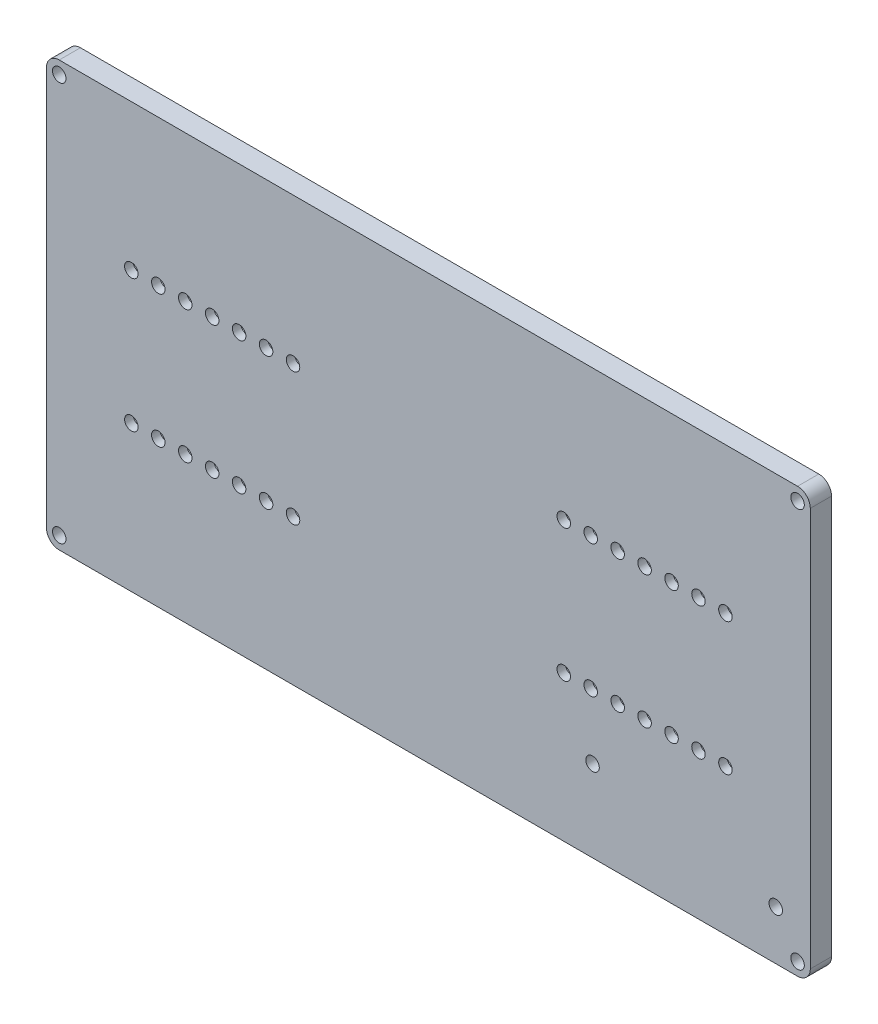
SolidWorks part; units mm, degrees
ref_plane "Front Plane" through (0, 0, 0) normal (0, 0, 1) x (1, 0, 0)
ref_plane "Top Plane" through (0, 0, 0) normal (0, 1, 0) x (1, 0, 0)
ref_plane "Right Plane" through (0, 0, 0) normal (1, 0, 0) x (0, 0, -1)
sketch "Sketch1" plane through (0, 0, 0) normal (0, 0, 1) x (1, 0, 0)
  line L0 (-90, 0) -> (90, 0) construction
  line L1 (-90, 50) -> (90, 50)
  line L2 (-90, 50) -> (-90, -50)
  line L3 (-90, -50) -> (90, -50)
  line L4 (90, 50) -> (90, -50)
  line L5 (-90, 50) -> (90, -50) construction
  line L6 (-90, -50) -> (90, 50) construction
  point P0 (0, 0)
  point P9 (0, 0)
  dimension "D1" = 100
  dimension "D2" = 180
extrude "Boss-Extrude1" add sketch "Sketch1" along normal blind 5 contours L1 L4 L3 L2
sketch "Sketch2" plane through (0, 0, 5) normal (0, 0, 1) x (1, 0, 0)
  line L0 (-90, 0) -> (90, 0) construction
  line L1 (-90, 50) -> (-90, -50) construction
  line L2 (90, 50) -> (90, -50) construction
  line L3 (0, 50) -> (0, -50) construction
  line L4 (-90, 50) -> (90, 50) construction
  line L5 (-90, -50) -> (90, -50) construction
  circle A0 centre (-70, 15.62) radius 1.59
  dimension "D1" = 3.18
  dimension "D2" = 70
  dimension "D3" = 15.62
extrude "Cut-Extrude1" cut sketch "Sketch2" against normal through all
pattern_linear "LPattern1" count 7 spacing 6.35 along (1, 0, 0) count 2 spacing 31.24 along (0, -1, 0) of "Cut-Extrude1"
ref_plane "Plane1" through (0, 0, 0) normal (1, 0, 0) x (0, 0, -1)
mirror "Mirror1" about plane through (0, 0, 0) normal (1, 0, 0) of "LPattern1", "Cut-Extrude1"
ref_plane "Plane2" through (0, 0, 0) normal (0, 1, 0) x (1, 0, 0)
sketch "Sketch4" plane through (0, 0, 0) normal (0, 0, -1) x (-1, 0, 0)
  line L0 (28.9, 15.62) -> (73, 15.62) construction
  line L1 (28.9, 18.22) -> (73, 18.22)
  line L2 (28.9, 18.22) -> (28.9, 13.02)
  line L3 (28.9, 13.02) -> (73, 13.02)
  line L4 (73, 18.22) -> (73, 13.02)
  circle A0 centre (70, 15.62) radius 1.59 construction
  circle A1 centre (70, 15.62) radius 1.59 construction
  circle A2 centre (31.9, 15.62) radius 1.59 construction
  circle A3 centre (31.9, 15.62) radius 1.59 construction
  dimension "D3" = 3
  dimension "D1" = 5.2
  dimension "D2" = 3
extrude "Cut-Extrude3" cut sketch "Sketch4" against normal blind 3
mirror "Mirror4" about plane through (0, 0, 0) normal (0, 1, 0) of "Cut-Extrude3"
mirror "Mirror5" about plane through (0, 0, 0) normal (1, 0, 0) of "Mirror4", "Cut-Extrude3"
fillet "Fillet1" radius 1 16 edges at (-28.9, -18.22, 1.5) (-28.9, -13.02, 1.5) (28.9, -13.02, 1.5) (73, -13.02, 1.5) (73, -18.22, 1.5) (28.9, -18.22, 1.5) (-73, -18.22, 1.5) (-73, -13.02, 1.5) (-73, 13.02, 1.5) (-73, 18.22, 1.5) (-28.9, 18.22, 1.5) (-28.9, 13.02, 1.5) (73, 13.02, 1.5) (73, 18.22, 1.5) (28.9, 13.02, 1.5) (28.9, 18.22, 1.5)
fillet "Fillet2" radius 3 4 edges at (90, -50, 2.5) (-90, -50, 2.5) (-90, 50, 2.5) (90, 50, 2.5)
sketch "Sketch5" plane through (0, 0, 0) normal (0, 0, -1) x (-1, 0, 0)
  line L1 (-81.8636, -38.3983) -> (-38.6836, -38.3983) construction
  line L2 (-81.8636, -38.3983) -> (-81.8636, -30.7783) construction
  line L3 (-81.8636, -30.7783) -> (-38.6836, -30.7783) construction
  line L4 (-38.6836, -38.3983) -> (-38.6836, -30.7783) construction
  circle A2 centre (-81.8636, -38.3983) radius 3
  circle A3 centre (-38.6836, -30.7783) radius 3
  dimension "D5" = 6
  dimension "D6" = 6
  dimension "D1" = 7.62
  dimension "D2" = 43.18
extrude "Boss-Extrude3" add sketch "Sketch5" along normal blind 3
sketch "Sketch11" plane through (0, 0, -3) normal (0, 0, -1) x (-1, 0, 0)
  circle A0 centre (-81.8636, -38.3983) radius 3 construction
  circle A1 centre (-81.8636, -38.3983) radius 3
  circle A2 centre (-81.8636, -38.3983) radius 1.59
  circle A3 centre (-38.6836, -30.7783) radius 1.59
  dimension "D1" = 3.18
  dimension "D2" = 3.18
extrude "Cut-Extrude5" cut sketch "Sketch11" against normal through all both and the other way through all contours A3 | A2
sketch "Sketch12" plane through (0, 0, 0) normal (0, 0, -1) x (-1, 0, 0)
  line L0 (-90, 47) -> (-90, -47) construction
  line L1 (-87, -47) -> (87, -47) construction
  line L2 (-87, -47) -> (-87, 47) construction
  line L3 (-87, 47) -> (87, 47) construction
  line L4 (87, -47) -> (87, 47) construction
  line L5 (87, 50) -> (-87, 50) construction
  line L6 (90, 47) -> (90, -47) construction
  line L7 (87, -50) -> (-87, -50) construction
  circle A0 centre (-87, -47) radius 1.59
  circle A1 centre (-87, 47) radius 1.59
  circle A2 centre (87, 47) radius 1.59
  circle A3 centre (87, -47) radius 1.59
  dimension "D1" = 3.18
  dimension "D2" = 3.18
  dimension "D3" = 3.18
  dimension "D4" = 3.18
  dimension "D5" = 3
  dimension "D6" = 3
  dimension "D7" = 3
  dimension "D8" = 3
extrude "Cut-Extrude6" cut sketch "Sketch12" against normal through all both and the other way through all
sketch "Sketch14" plane through (0, 0, 0) normal (0, 0, -1) x (-1, 0, 0)
  line L0 (-89, 45.3483) -> (-89, -45.3544)
  line L1 (-85.3544, -49) -> (85.3544, -49)
  line L2 (89, -45.3544) -> (89, 45.3544)
  line L3 (85.3544, 49) -> (-85.3483, 49)
  line L4 (-73, -14.02) -> (-73, -17.22) construction
  line L5 (73, -14.02) -> (73, -17.22) construction
  line L6 (-29.9, -13.02) -> (-72, -13.02) construction
  line L7 (-73, 14.02) -> (-73, 17.22) construction
  line L8 (-72, -18.22) -> (-29.9, -18.22) construction
  line L9 (-28.9, -17.22) -> (-28.9, -14.02) construction
  line L10 (-29.9, -12.02) -> (-72, -12.02)
  line L11 (29.9, -13.02) -> (72, -13.02) construction
  line L12 (72, -18.22) -> (29.9, -18.22) construction
  line L13 (28.9, -17.22) -> (28.9, -14.02) construction
  line L14 (73, 14.02) -> (73, 17.22) construction
  line L15 (-29.9, 13.02) -> (-72, 13.02) construction
  line L16 (-72, 18.22) -> (-29.9, 18.22) construction
  line L17 (-28.9, 17.22) -> (-28.9, 14.02) construction
  line L18 (-29.9, 13.02) -> (-72, 13.02) construction
  line L19 (-73, 14.02) -> (-73, 17.22) construction
  line L20 (-72, 18.22) -> (-29.9, 18.22) construction
  line L21 (74, -17.22) -> (74, -14.02)
  line L22 (-73, -14.02) -> (-73, -17.22) construction
  line L23 (-28.9, -17.22) -> (-28.9, -14.02) construction
  line L24 (-72, -18.22) -> (-29.9, -18.22) construction
  line L25 (-29.9, -13.02) -> (-72, -13.02) construction
  line L26 (29.9, 13.02) -> (72, 13.02) construction
  line L27 (28.9, 17.22) -> (28.9, 14.02) construction
  line L28 (72, 18.22) -> (29.9, 18.22) construction
  line L29 (73, -14.02) -> (73, -17.22) construction
  line L30 (29.9, -13.02) -> (72, -13.02) construction
  line L31 (72, -18.22) -> (29.9, -18.22) construction
  line L32 (28.9, -17.22) -> (28.9, -14.02) construction
  line L33 (73, 14.02) -> (73, 17.22) construction
  line L34 (29.9, 13.02) -> (72, 13.02) construction
  line L35 (28.9, 17.22) -> (28.9, 14.02) construction
  line L36 (72, 18.22) -> (29.9, 18.22) construction
  line L37 (72, -12.02) -> (29.9, -12.02)
  line L38 (27.9, -14.02) -> (27.9, -14.5041)
  line L39 (72, -19.22) -> (36.6294, -19.22)
  line L40 (74, 17.22) -> (74, 14.02)
  line L41 (72, 19.22) -> (36.6294, 19.22)
  line L42 (27.9, 17.22) -> (27.9, 15.6407)
  line L43 (29.9, 12.02) -> (72, 12.02)
  line L44 (-27.9, 14.02) -> (-27.9, 14.5041)
  line L45 (-29.9, 19.22) -> (-34.5255, 19.22)
  line L46 (-74, 17.22) -> (-74, 14.02)
  line L47 (-29.9, 12.02) -> (-72, 12.02)
  line L48 (-74, -14.02) -> (-74, -17.22)
  line L49 (-72, -19.22) -> (-36.6294, -19.22)
  line L50 (-27.9, -14.02) -> (-27.9, -14.5041)
  line L51 (-87, 47) -> (87, -47) construction
  line L52 (87, 47) -> (-87, -47) construction
  line L53 (0.0031, 49) -> (0, -49) construction
  line L54 (-85.0018, -45.3522) -> (-36.6294, -19.22)
  line L55 (-84.5265, -46.232) -> (-34.5255, -19.22)
  line L56 (-89, -0.0031) -> (89, 0) construction
  line L57 (34.5255, -19.22) -> (84.5265, -46.232)
  line L58 (85.0018, -45.3522) -> (36.6294, -19.22)
  line L59 (-84.523, 46.2301) -> (-34.5255, 19.22)
  line L60 (-84.9983, 45.3503) -> (-36.6294, 19.22)
  line L61 (34.5255, 19.22) -> (84.5265, 46.232)
  line L62 (36.6294, 19.22) -> (85.0018, 45.3522)
  line L63 (87, 50) -> (-87, 50) construction
  line L64 (-90, 47) -> (-90, -47) construction
  line L65 (90, 47) -> (90, -47) construction
  line L66 (87, -50) -> (-87, -50) construction
  line L67 (39.8193, 22.0799) -> (40.2946, 21.2001) construction
  line L68 (-51.9381, 27.4902) -> (-51.4628, 28.3701) construction
  line L69 (-56.6413, -30.031) -> (-56.166, -30.9109) construction
  line L70 (52.5149, -28.9384) -> (52.9902, -28.0586) construction
  line L71 (-34.5255, -19.22) -> (-29.9, -19.22)
  line L72 (-36.6294, 19.22) -> (-72, 19.22)
  line L73 (34.5255, 19.22) -> (29.9, 19.22)
  line L74 (34.5255, -19.22) -> (29.9, -19.22)
  line L75 (-27.9, 15.6407) -> (-0.7963, 0.9985)
  line L76 (27.9, -15.6407) -> (0.8019, -1.0015)
  line L77 (27.9, 15.6407) -> (0.7963, 0.9985)
  line L78 (27.9, 14.5041) -> (2.9003, 0.9985)
  line L79 (-21.5483, -11.0728) -> (-21.073, -11.9526) construction
  line L80 (8.7172, -5.2776) -> (9.1925, -4.3978) construction
  line L81 (-1.052, 0) -> (-1.0548, -0.0015)
  line L82 (1.052, 0) -> (1.0547, -0.0015)
  line L83 (0.0015, -0.5675) -> (0, -0.5683)
  line L84 (-1.0491, -0.0015) -> (-1.052, 0)
  line L85 (-27.9, 15.6407) -> (-27.9, 17.22)
  line L86 (27.9, 14.5041) -> (27.9, 14.02)
  line L87 (27.9, -15.6407) -> (27.9, -17.22)
  line L88 (-27.9, -15.6407) -> (-27.9, -17.22)
  line L89 (-89, 0.9969) -> (-2.9001, 0.9984)
  line L90 (89, -1) -> (2.9058, -1.0015)
  line L91 (-77.7041, 0.9971) -> (-77.7041, -1.0029) construction
  line L92 (-2.9001, 0.9984) -> (-27.9, 14.5041)
  line L93 (0, 0.5683) -> (0.0015, 0.5675)
  line L94 (0.0015, 0.5691) -> (0, 0.5683)
  line L95 (1.052, 0) -> (1.0492, -0.0015)
  line L96 (2.9058, -1.0015) -> (27.9, -14.5041)
  line L97 (0.0015, -0.5691) -> (0, -0.5683)
  line L98 (-0.802, -1.0015) -> (-27.9, -15.6407)
  line L99 (-2.9059, -1.0016) -> (-27.9, -14.5041)
  line L100 (-0.7963, 0.9985) -> (0.7963, 0.9985)
  line L101 (2.9003, 0.9985) -> (89, 1)
  line L102 (-2.9059, -1.0016) -> (-89, -1.0031)
  line L103 (0.8019, -1.0015) -> (-0.802, -1.0015)
  arc A0 (-89, -45.3544) -> (-85.3544, -49) centre (-87, -47) cw
  arc A1 (85.3544, -49) -> (89, -45.3544) centre (87, -47) cw
  arc A2 (85.3544, 49) -> (89, 45.3544) centre (87, 47) ccw
  arc A3 (-85.3483, 49) -> (-89, 45.3483) centre (-87, 47) cw
  arc A4 (72, -18.22) -> (73, -17.22) centre (72, -17.22) ccw construction
  arc A5 (73, -14.02) -> (72, -13.02) centre (72, -14.02) ccw construction
  arc A6 (28.9, -17.22) -> (29.9, -18.22) centre (29.9, -17.22) ccw construction
  arc A7 (29.9, -13.02) -> (28.9, -14.02) centre (29.9, -14.02) ccw construction
  arc A8 (73, 17.22) -> (72, 18.22) centre (72, 17.22) ccw construction
  arc A9 (72, 13.02) -> (73, 14.02) centre (72, 14.02) ccw construction
  arc A10 (28.9, 14.02) -> (29.9, 13.02) centre (29.9, 14.02) ccw construction
  arc A11 (29.9, 18.22) -> (28.9, 17.22) centre (29.9, 17.22) ccw construction
  arc A12 (72, -18.22) -> (73, -17.22) centre (72, -17.22) ccw construction
  arc A13 (73, -14.02) -> (72, -13.02) centre (72, -14.02) ccw construction
  arc A14 (28.9, -17.22) -> (29.9, -18.22) centre (29.9, -17.22) ccw construction
  arc A15 (29.9, -13.02) -> (28.9, -14.02) centre (29.9, -14.02) ccw construction
  arc A16 (73, 17.22) -> (72, 18.22) centre (72, 17.22) ccw construction
  arc A17 (72, 13.02) -> (73, 14.02) centre (72, 14.02) ccw construction
  arc A18 (28.9, 14.02) -> (29.9, 13.02) centre (29.9, 14.02) ccw construction
  arc A19 (29.9, 18.22) -> (28.9, 17.22) centre (29.9, 17.22) ccw construction
  arc A20 (-72, -13.02) -> (-73, -14.02) centre (-72, -14.02) ccw construction
  arc A21 (-73, -17.22) -> (-72, -18.22) centre (-72, -17.22) ccw construction
  arc A22 (-29.9, -18.22) -> (-28.9, -17.22) centre (-29.9, -17.22) ccw construction
  arc A23 (-28.9, -14.02) -> (-29.9, -13.02) centre (-29.9, -14.02) ccw construction
  arc A24 (-72, -13.02) -> (-73, -14.02) centre (-72, -14.02) ccw construction
  arc A25 (-73, -17.22) -> (-72, -18.22) centre (-72, -17.22) ccw construction
  arc A26 (-28.9, -14.02) -> (-29.9, -13.02) centre (-29.9, -14.02) ccw construction
  arc A27 (-29.9, -18.22) -> (-28.9, -17.22) centre (-29.9, -17.22) ccw construction
  arc A28 (-72, 18.22) -> (-73, 17.22) centre (-72, 17.22) ccw construction
  arc A29 (-28.9, 17.22) -> (-29.9, 18.22) centre (-29.9, 17.22) ccw construction
  arc A30 (-29.9, 13.02) -> (-28.9, 14.02) centre (-29.9, 14.02) ccw construction
  arc A31 (-73, 14.02) -> (-72, 13.02) centre (-72, 14.02) ccw construction
  arc A32 (-28.9, 17.22) -> (-29.9, 18.22) centre (-29.9, 17.22) ccw construction
  arc A33 (-29.9, 13.02) -> (-28.9, 14.02) centre (-29.9, 14.02) ccw construction
  arc A34 (-73, 14.02) -> (-72, 13.02) centre (-72, 14.02) ccw construction
  arc A35 (-72, 18.22) -> (-73, 17.22) centre (-72, 17.22) ccw construction
  arc A36 (-74, 17.22) -> (-72, 19.22) centre (-72, 17.22) cw
  arc A37 (-29.9, 19.22) -> (-27.9, 17.22) centre (-29.9, 17.22) cw
  arc A38 (-27.9, 14.02) -> (-29.9, 12.02) centre (-29.9, 14.02) cw
  arc A39 (-72, 12.02) -> (-74, 14.02) centre (-72, 14.02) cw
  arc A40 (-27.9, -17.22) -> (-29.9, -19.22) centre (-29.9, -17.22) cw
  arc A41 (-27.9, -14.02) -> (-29.9, -12.02) centre (-29.9, -14.02) ccw
  arc A42 (-72, -12.02) -> (-74, -14.02) centre (-72, -14.02) ccw
  arc A43 (-72, -19.22) -> (-74, -17.22) centre (-72, -17.22) cw
  arc A44 (29.9, -19.22) -> (27.9, -17.22) centre (29.9, -17.22) cw
  arc A45 (27.9, -14.02) -> (29.9, -12.02) centre (29.9, -14.02) cw
  arc A46 (74, 17.22) -> (72, 19.22) centre (72, 17.22) ccw
  arc A47 (72, 12.02) -> (74, 14.02) centre (72, 14.02) ccw
  arc A48 (29.9, 19.22) -> (27.9, 17.22) centre (29.9, 17.22) ccw
  arc A49 (27.9, 14.02) -> (29.9, 12.02) centre (29.9, 14.02) ccw
  arc A50 (72, -12.02) -> (74, -14.02) centre (72, -14.02) cw
  arc A51 (74, -17.22) -> (72, -19.22) centre (72, -17.22) cw
  circle A52 centre (-87, 47) radius 1.59 construction
  circle A53 centre (87, 47) radius 1.59 construction
  circle A54 centre (87, -47) radius 1.59 construction
  circle A55 centre (-87, -47) radius 1.59 construction
  point P135 (-51.7005, 27.9302)
  point P139 (-56.4037, -30.471)
  point P141 (52.7526, -28.4985)
  point P146 (40.057, 21.64)
  point P155 (-21.3107, -11.5127)
  point P159 (8.9549, -4.8377)
  point P173 (-77.7041, -0.0029)
  dimension "D3" = 1.0039
  dimension "D7" = 1
  dimension "D8" = 1
  dimension "D11" = 1
  dimension "D15" = 1
  dimension "D1" = 1
  dimension "D2" = 1
  dimension "D4" = 1
  dimension "D5" = 1
  dimension "D6" = 1
  dimension "D9" = 1
  dimension "D10" = 1
  dimension "D12" = 1
  dimension "D13" = 1
  dimension "D14" = 1
  dimension "D16" = 1
  dimension "D17" = 1
  dimension "D18" = 1
  dimension "D19" = 2
extrude "Cut-Extrude7" cut sketch "Sketch14" against normal blind 4
sketch "Sketch15" plane through (0, 0, 4) normal (0, 0, -1) x (-1, 0, 0)
  line L0 (72.3513, 47.9244) -> (46.4109, 47.9244) construction
  text T0 "REV 1" font "Consolas" height 5
extrude "Cut-Extrude8" cut sketch "Sketch15" against normal blind 0.4
